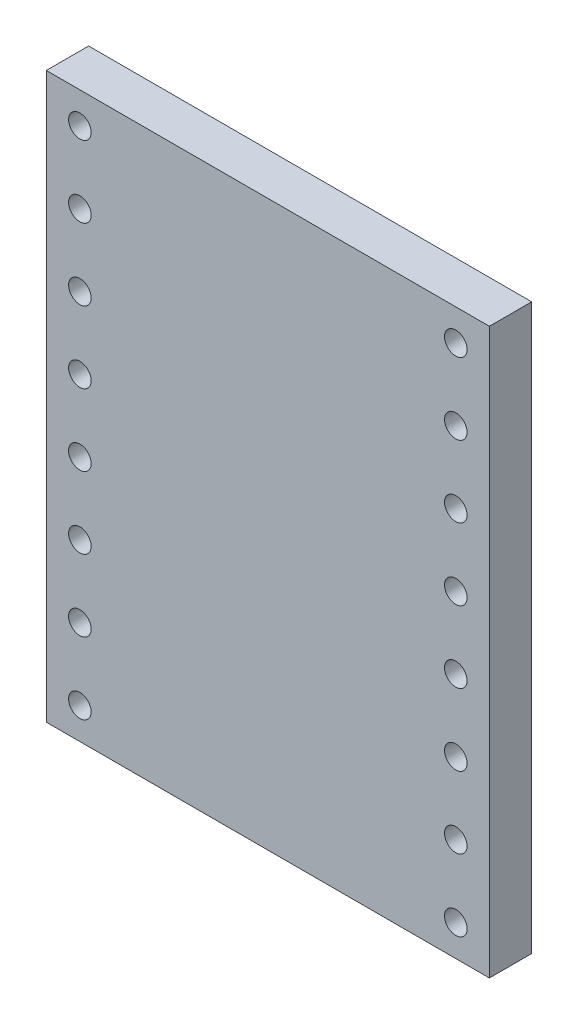
SolidWorks part; units mm, degrees
ref_plane "Piano frontale" through (0, 0, 0) normal (0, 0, 1) x (1, 0, 0)
ref_plane "Piano superiore" through (0, 0, 0) normal (0, 1, 0) x (1, 0, 0)
ref_plane "Piano destro" through (0, 0, 0) normal (1, 0, 0) x (0, 0, -1)
sketch "Schizzo1" plane through (0, 0, 0) normal (0, 0, 1) x (1, 0, 0)
  line L1 (-7.85, -10) -> (7.85, -10)
  line L2 (-7.85, -10) -> (-7.85, 10)
  line L3 (-7.85, 10) -> (7.85, 10)
  line L4 (7.85, -10) -> (7.85, 10)
  line L5 (-7.85, -10) -> (7.85, 10) construction
  line L6 (-7.85, 10) -> (7.85, -10) construction
  point P0 (0, 0)
  dimension "D1" = 15.7
  dimension "D2" = 20
extrude "Estrusione-Estrusione1" add sketch "Schizzo1" along normal blind 1.5
sketch "Schizzo2" plane through (0, 0, 1.5) normal (0, 0, 1) x (1, 0, 0)
  line L0 (7.85, 10) -> (-7.85, 10) construction
  line L1 (0, 0) -> (0, 2.2289) construction
  line L2 (-7.85, 10) -> (-7.85, -10) construction
  circle A0 centre (-6.66, 8.89) radius 0.4
  circle A1 centre (-6.66, 6.35) radius 0.4
  circle A2 centre (-6.66, 3.81) radius 0.4
  circle A3 centre (-6.66, 1.27) radius 0.4
  circle A4 centre (-6.66, -1.27) radius 0.4
  circle A5 centre (-6.66, -3.81) radius 0.4
  circle A6 centre (-6.66, -6.35) radius 0.4
  circle A7 centre (-6.66, -8.89) radius 0.4
  circle A8 centre (6.66, -8.89) radius 0.4
  circle A9 centre (6.66, -6.35) radius 0.4
  circle A10 centre (6.66, -3.81) radius 0.4
  circle A11 centre (6.66, -1.27) radius 0.4
  circle A12 centre (6.66, 1.27) radius 0.4
  circle A13 centre (6.66, 3.81) radius 0.4
  circle A14 centre (6.66, 6.35) radius 0.4
  circle A15 centre (6.66, 8.89) radius 0.4
  dimension "D1" = 0.8
  dimension "D2" = 2.54
  dimension "D3" = 2.54
  dimension "D4" = 2.54
  dimension "D5" = 2.54
  dimension "D6" = 2.54
  dimension "D7" = 2.54
  dimension "D8" = 2.54
  dimension "D11" = 1.11
  dimension "D12" = 1.19
  dimension "D9" = 1.27
  dimension "D10" = 6.66
extrude "Taglio-Estrusione1" cut sketch "Schizzo2" against normal blind 1.5
